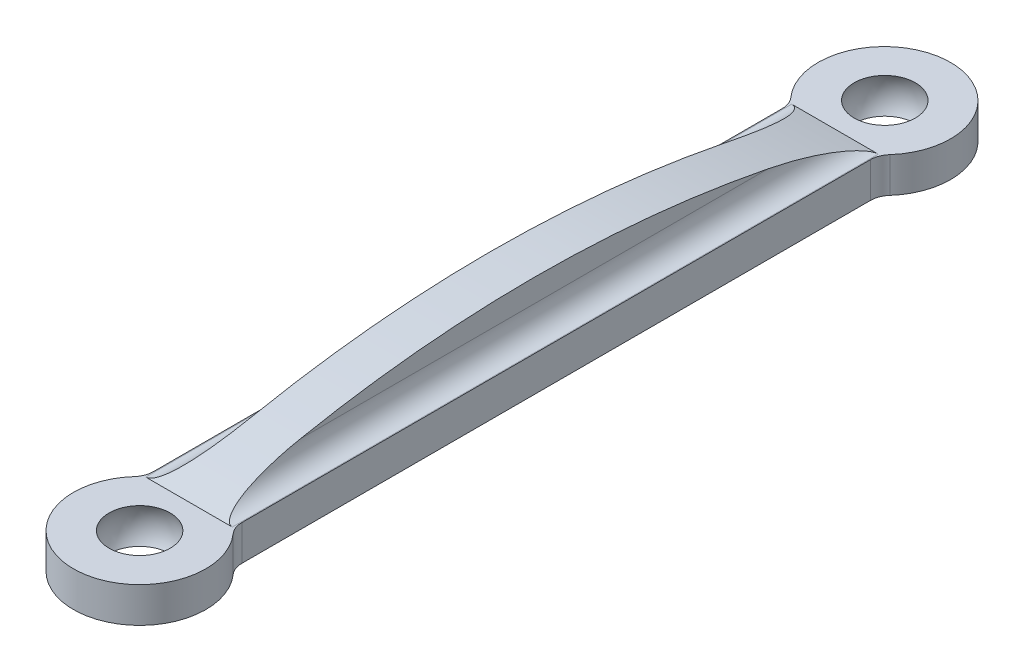
SolidWorks part; units mm, degrees
material "ABS"
ref_plane "Front Plane" through (0, 0, 0) normal (0, 0, 1) x (1, 0, 0)
ref_plane "Top Plane" through (0, 0, 0) normal (0, 1, 0) x (1, 0, 0)
ref_plane "Right Plane" through (0, 0, 0) normal (1, 0, 0) x (0, 0, -1)
sketch "Sketch1" plane through (0, 0, 0) normal (0, 1, 0) x (1, 0, 0)
  line L0 (0, 53.5432) -> (0, 0) construction
  line L3 (-3.175, 3.5498) -> (-3.175, 49.9934)
  line L4 (3.175, 49.9934) -> (3.175, 3.5498)
  circle A0 centre (0, 0) radius 1.5875
  circle A1 centre (0, 53.5432) radius 1.5875
  arc A4 (3.175, 49.9934) -> (-3.175, 49.9934) centre (0, 53.5432) ccw
  arc A5 (-3.175, 3.5498) -> (3.175, 3.5498) centre (0, 0) ccw
  point P5 (0, 26.7716)
  dimension "D1" = 3.175
  dimension "D2" = 3.175
  dimension "D4" = 9.525
  dimension "D3" = 53.5432
  dimension "D5" = 6.35
extrude "Boss-Extrude1" add sketch "Sketch1" along normal mid plane 2.54
sketch "Sketch2" plane through (0, 0, 0) normal (1, 0, 0) x (0, 0, -1)
  line L0 (0, -2.54) -> (0, 2.54)
  arc A0 (0, 2.54) -> (0, -2.54) centre (0, 0) cw
  dimension "D1" = 2.54
revolve "Cut-Revolve1" cut sketch "Sketch2" angle 360 about L0
sketch "Sketch3" plane through (0, 0, 0) normal (1, 0, 0) x (0, 0, -1)
  line L5 (53.5745, 8.5087) -> (53.5745, -3.7708)
  arc A0 (53.5745, 2.54) -> (53.5745, -2.54) centre (53.5745, 0) ccw
  dimension "D1" = 2.54
revolve "Cut-Revolve2" cut sketch "Sketch3" angle 360 about L5
sketch "Sketch5" plane through (0, 0, 0) normal (1, 0, 0) x (0, 0, -1)
  line L0 (3.5498, 1.27) -> (49.9934, 1.27) construction
  line L1 (3.5498, 4.445) -> (49.9934, 4.445) construction
  line L2 (3.5498, 1.27) -> (49.9934, 1.27)
  arc A0 (3.5498, 1.27) -> (49.9934, 1.27) centre (26.7716, -82.0644) cw
  dimension "D1" = 3.175
extrude "Boss-Extrude2" add sketch "Sketch5" along normal mid plane 3.175
fillet "Fillet1" radius 1.524 6 edges at (-3.175, 0, -49.9934) (3.175, 0, -49.9934) (1.5875, 1.27, -26.7716) (-1.5875, 1.27, -26.7716) (-3.175, 0, -3.5498) (3.175, 0, -3.5498)
